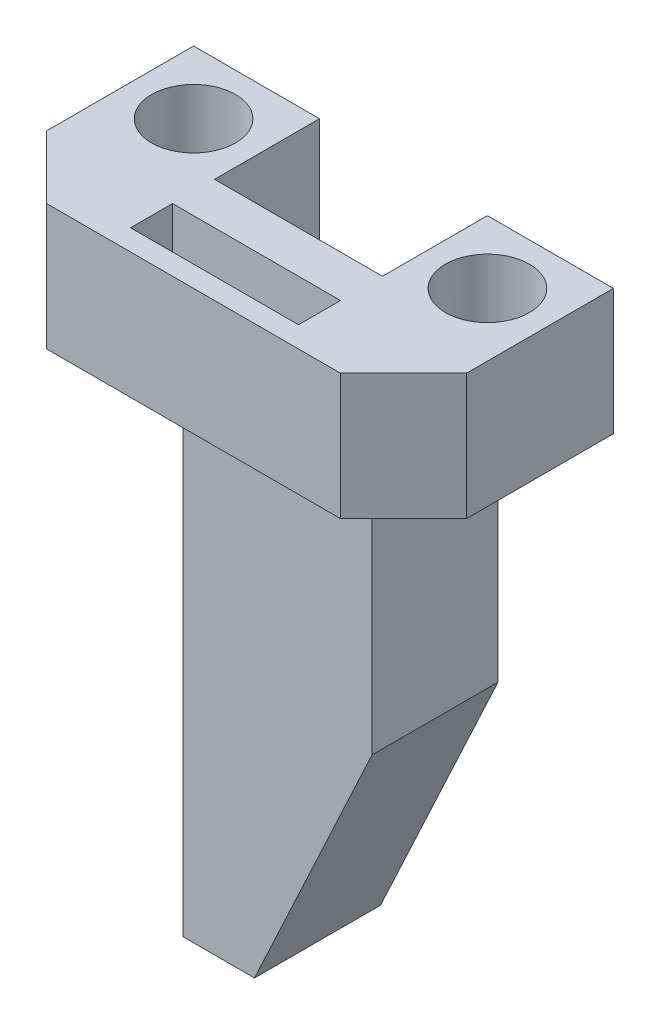
SolidWorks part; units mm, degrees
ref_plane "前视基准面" through (0, 0, 0) normal (0, 0, 1) x (1, 0, 0)
ref_plane "上视基准面" through (0, 0, 0) normal (0, 1, 0) x (1, 0, 0)
ref_plane "右视基准面" through (0, 0, 0) normal (1, 0, 0) x (0, 0, -1)
sketch "草图1" plane through (0, 0, 0) normal (0, 1, 0) x (1, 0, 0)
  line L0 (-4, 5) -> (-4, 10)
  line L1 (-10, 0) -> (10, 0)
  line L2 (-10, 0) -> (-10, 5)
  line L3 (-4, 5) -> (4, 5)
  line L4 (10, 0) -> (10, 5)
  line L5 (-4, 10) -> (-10, 10)
  line L6 (-10, 10) -> (-10, 5)
  line L7 (0, 0) -> (0, 5) construction
  line L8 (4, 5) -> (4, 10)
  line L9 (4, 10) -> (10, 10)
  line L10 (10, 10) -> (10, 5)
  dimension "D1" = 5
  dimension "D2" = 4
  dimension "D3" = 5
  dimension "D4" = 6
extrude "凸台-拉伸1" add sketch "草图1" along normal blind 6
sketch "草图2" plane through (0, 6, 0) normal (0, 1, 0) x (1, 0, 0)
  line L0 (0, 0) -> (0, 5) construction
  line L1 (-10, 0) -> (10, 0) construction
  line L2 (4, 5) -> (-4, 5) construction
  line L4 (-4, 10) -> (-10, 10) construction
  line L5 (-10, 10) -> (-10, 0) construction
  line L6 (4, 3) -> (4, 1)
  line L7 (-4, 3) -> (4, 3)
  line L8 (-4, 3) -> (-4, 1)
  line L9 (-4, 1) -> (4, 1)
  circle A0 centre (-7, 7) radius 2
  circle A1 centre (7, 7) radius 2
  point P17 (0, 1)
  point P20 (0, 3)
  dimension "D1" = 4
  dimension "D2" = 3
  dimension "D3" = 3
  dimension "D4" = 2
  dimension "D5" = 4
  dimension "D6" = 2
extrude "切除-拉伸3" cut sketch "草图2" against normal up to next
chamfer "倒角1" distance 3 angle 45 2 edges at (10, 3, 0) (-10, 3, 0)
sketch "草图5" plane through (0, 0, 0) normal (0, -1, 0) x (1, 0, 0)
  line L1 (-4.5, -4) -> (4.5, -4)
  line L2 (0, 0) -> (0, -10) construction
  line L3 (-4.5, -10) -> (4.5, -10)
  line L4 (-4.5, -4) -> (-4.5, -10)
  line L10 (-4, -10) -> (-10, -10) construction
  line L11 (4.5, -4) -> (4.5, -10)
  point P10 (0, -4)
  dimension "D1" = 6
  dimension "D2" = 4.5
extrude "凸台-拉伸5" add sketch "草图5" along normal blind 25
chamfer "倒角3" distance 12 angle 25 1 edges at (4.5, -25, -7)
